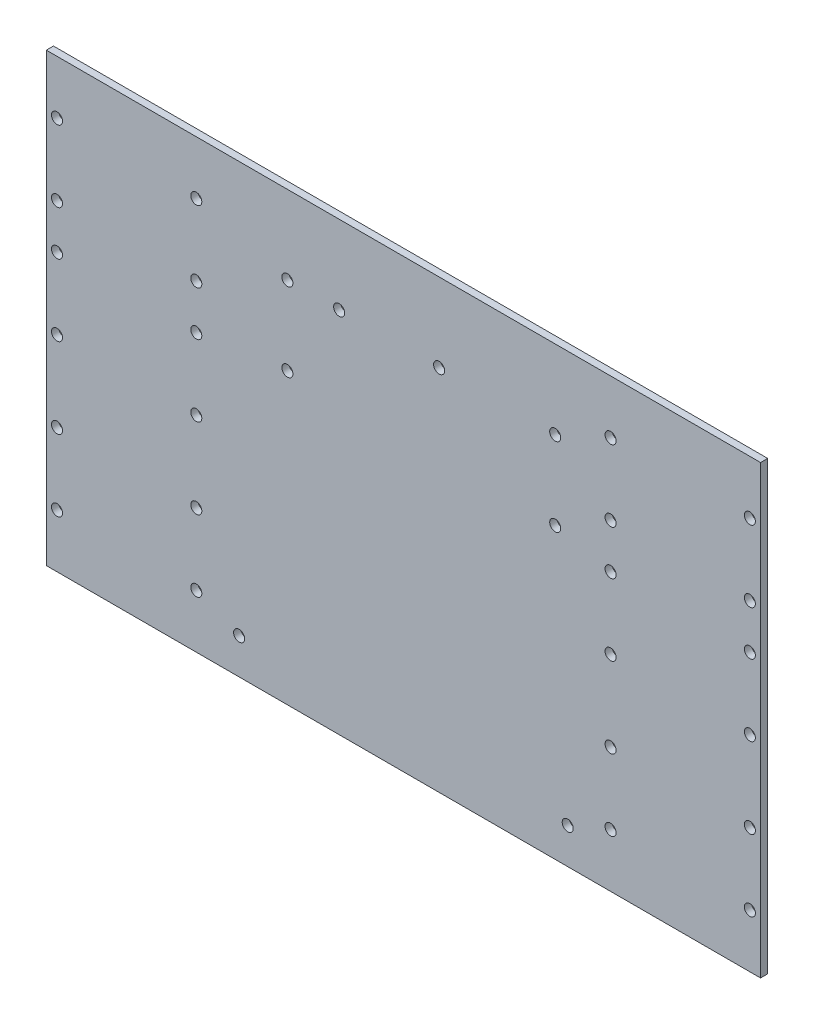
SolidWorks part; units mm, degrees
material "Thornel Mat VMA"
ref_plane "前视基准面" through (0, 0, 0) normal (0, 0, 1) x (1, 0, 0)
ref_plane "上视基准面" through (0, 0, 0) normal (0, 1, 0) x (1, 0, 0)
ref_plane "右视基准面" through (0, 0, 0) normal (1, 0, 0) x (0, 0, -1)
sketch "草图1" plane through (0, 0, 0) normal (0, 0, 1) x (1, 0, 0)
  line L0 (-119.8388, 0) -> (119.8388, 0) construction
  line L1 (-100, 62.5) -> (100, 62.5)
  line L2 (-100, 62.5) -> (-100, -62.5)
  line L3 (-100, -62.5) -> (100, -62.5)
  line L4 (100, 62.5) -> (100, -62.5)
  line L5 (-100, 62.5) -> (100, -62.5) construction
  line L6 (-100, -62.5) -> (100, 62.5) construction
  line L7 (0, 131.1183) -> (0, -131.1183) construction
  line L8 (-32.5, 40.5) -> (42.5, 40.5) construction
  circle A0 centre (-97, -47.5) radius 1.55
  circle A1 centre (-97, -27.5) radius 1.55
  circle A2 centre (-97, 47.5) radius 1.55
  circle A3 centre (-97, 27.5) radius 1.55
  circle A4 centre (-97, -5) radius 1.55
  circle A5 centre (-97, 15) radius 1.55
  circle A6 centre (97, 47.5) radius 1.55
  circle A7 centre (97, 27.5) radius 1.55
  circle A10 centre (97, -27.5) radius 1.55
  circle A11 centre (97, -47.5) radius 1.55
  circle A12 centre (-58, 47.5) radius 1.55
  circle A15 centre (-58, 27.5) radius 1.55
  circle A16 centre (-58, -27.5) radius 1.55
  circle A17 centre (-58, -47.5) radius 1.55
  circle A18 centre (58, 47.5) radius 1.55
  circle A19 centre (58, 27.5) radius 1.55
  circle A20 centre (58, -47.5) radius 1.55
  circle A21 centre (58, -27.5) radius 1.55
  circle A22 centre (-58, -5) radius 1.55
  circle A23 centre (-58, 15) radius 1.55
  circle A24 centre (97, 15) radius 1.55
  circle A25 centre (97, -5) radius 1.55
  circle A26 centre (58, 15) radius 1.55
  circle A27 centre (58, -5) radius 1.55
  circle A28 centre (-32.5, 40.5) radius 1.55
  circle A29 centre (-32.5, 18.5) radius 1.55
  circle A30 centre (-18, 40.5) radius 1.55
  circle A31 centre (10, 40.5) radius 1.55
  circle A32 centre (42.5, 40.5) radius 1.55
  circle A33 centre (42.5, 18.5) radius 1.55
  circle A34 centre (-46, -52.5) radius 1.55
  circle A35 centre (46, -52.5) radius 1.55
  point P0 (0, 0)
  point P9 (0, 0)
  point P66 (0, 0)
  point P73 (5, 40.5)
  dimension "D3" = 15
  dimension "D11" = 3
  dimension "D16" = 42
  dimension "D17" = 42
  dimension "D18" = 14.5
  dimension "D25" = 10
  dimension "D29" = 20
  dimension "D1" = 200
  dimension "D2" = 125
  dimension "D4" = 20
  dimension "D5" = 3
  dimension "D6" = 3
  dimension "D7" = 3
  dimension "D8" = 3
  dimension "D9" = 15
  dimension "D10" = 20
  dimension "D12" = 3
  dimension "D13" = 5
  dimension "D14" = 15
  dimension "D15" = 3
  dimension "D19" = 28
  dimension "D20" = 32.5
  dimension "D21" = 22
  dimension "D22" = 22
  dimension "D23" = 22
  dimension "D24" = 5
  dimension "D26" = 10
  dimension "D27" = 13.5
  dimension "D28" = 3.5
  dimension "D30" = 20
  dimension "D31" = 20
  dimension "D32" = 15
  dimension "D33" = 15
extrude "凸台-拉伸1" add sketch "草图1" along normal blind 2
